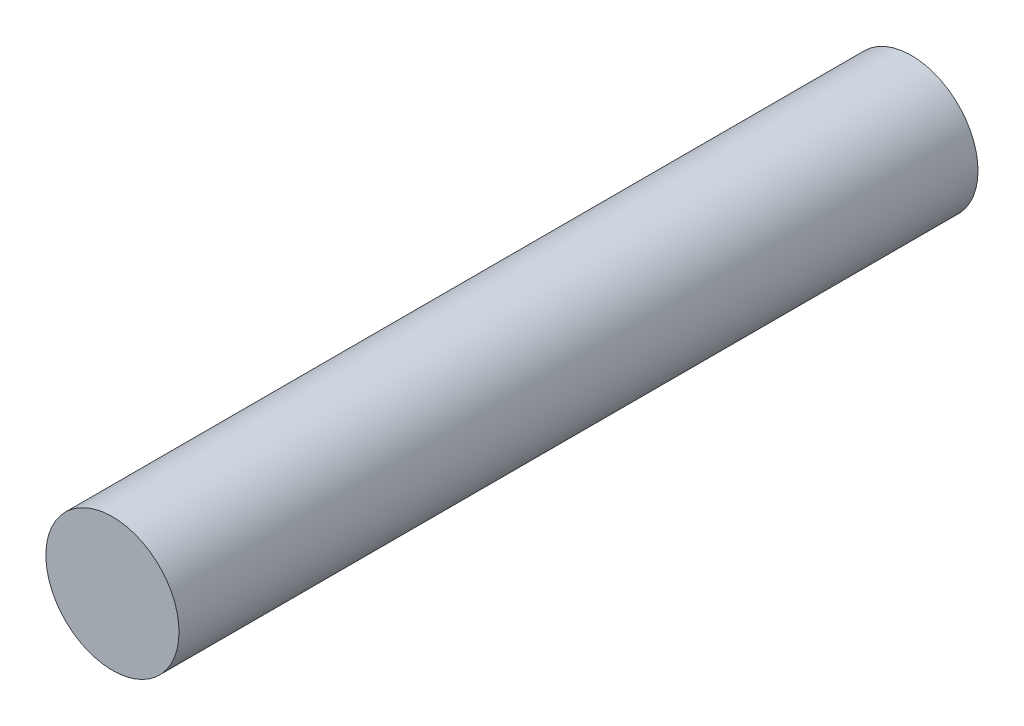
SolidWorks part; units mm, degrees
ref_plane "Ön Düzlem" through (0, 0, 0) normal (0, 0, 1) x (1, 0, 0)
ref_plane "Üst Düzlem" through (0, 0, 0) normal (0, 1, 0) x (1, 0, 0)
ref_plane "Sağ Düzlem" through (0, 0, 0) normal (1, 0, 0) x (0, 0, -1)
sketch "Çizim1" plane through (0, 0, 0) normal (0, 0, 1) x (1, 0, 0)
  circle A0 centre (0, 0) radius 2.5
  dimension "D1" = 5
extrude "Yükseklik-Ekstrüzyon1" add sketch "Çizim1" along normal mid plane 30
